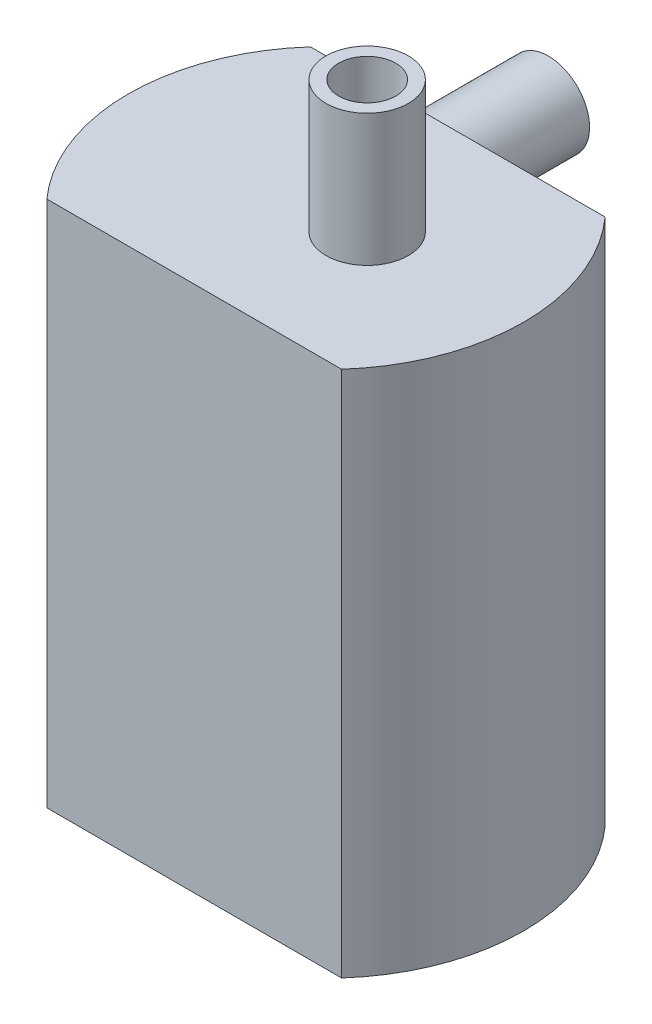
SolidWorks part; units mm, degrees
material "ABS"
ref_plane "Front" through (0, 0, 0) normal (0, 0, 1) x (1, 0, 0)
ref_plane "Top" through (0, 0, 0) normal (0, 1, 0) x (1, 0, 0)
ref_plane "Right" through (0, 0, 0) normal (1, 0, 0) x (0, 0, -1)
sketch "Sketch1" plane through (0, 0, 0) normal (0, 1, 0) x (1, 0, 0)
  line L0 (-14.199, 12.7) -> (14.199, 12.7)
  line L1 (-14.199, -12.7) -> (14.199, -12.7)
  circle A0 centre (0, 0) radius 19.05
  point P7 (0, 0)
  point P8 (0, 0)
  point P9 (0, 0)
  point P10 (0, 0)
  point P11 (0, 0)
  dimension "D1" = 38.1
  dimension "D2" = 25.4
extrude "Boss-Extrude2" add sketch "Sketch1" along normal blind 50.8 contours L1 A0 L0
sketch "Sketch2" plane through (0, 50.8, 0) normal (0, 1, 0) x (1, 0, 0)
  circle A0 centre (3.9688, 0) radius 3.9688
  circle A1 centre (3.9688, 0) radius 2.75
  dimension "D1" = 7.9375
  dimension "D3" = 5.5
  dimension "D2" = 3.9688
extrude "Boss-Extrude3" add sketch "Sketch2" along normal blind 12.7
sketch "Sketch3" plane through (0, 0, -12.7) normal (0, 0, -1) x (-1, 0, 0)
  line L0 (14.199, 50.8) -> (-14.199, 50.8) construction
  circle A0 centre (3.9688, 44.8312) radius 3.9688
  circle A1 centre (3.9688, 44.8312) radius 2.75
  point P4 (0, 50.8)
  dimension "D1" = 7.9375
  dimension "D4" = 5.5
  dimension "D2" = 3.9688
  dimension "D3" = 5.9688
extrude "Boss-Extrude4" add sketch "Sketch3" along normal blind 12.7
